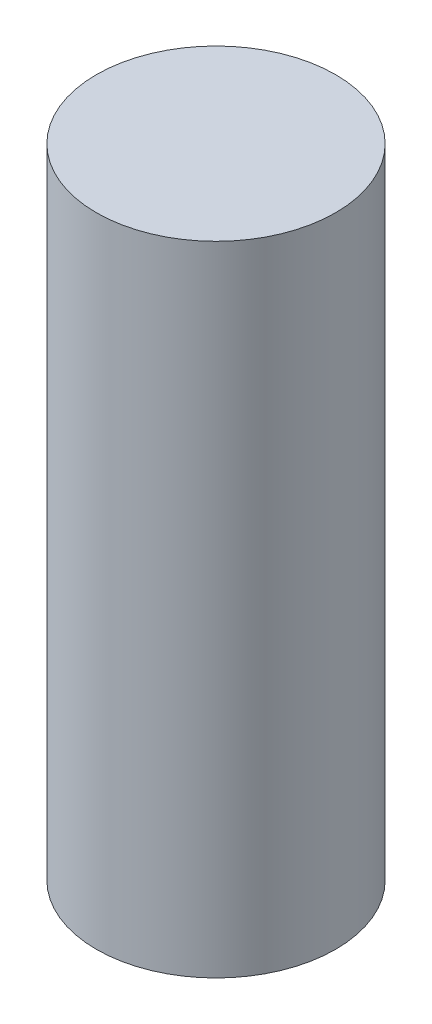
SolidWorks part; units mm, degrees
ref_plane "Front Plane" through (0, 0, 0) normal (0, 0, 1) x (1, 0, 0)
ref_plane "Top Plane" through (0, 0, 0) normal (0, 1, 0) x (1, 0, 0)
ref_plane "Right Plane" through (0, 0, 0) normal (1, 0, 0) x (0, 0, -1)
sketch "Sketch1" plane through (0, 0, 0) normal (0, 0, 1) x (1, 0, 0)
  line L0 (0, 0) -> (0, 44.5128) construction
  line L2 (0, 0) -> (15, 0)
  line L3 (0, 0) -> (0, 80)
  line L4 (0, 80) -> (15, 80)
  line L5 (15, 0) -> (15, 80)
  dimension "D1" = 15
  dimension "D2" = 80
revolve "Revolve1" add sketch "Sketch1" angle 360 about L0
